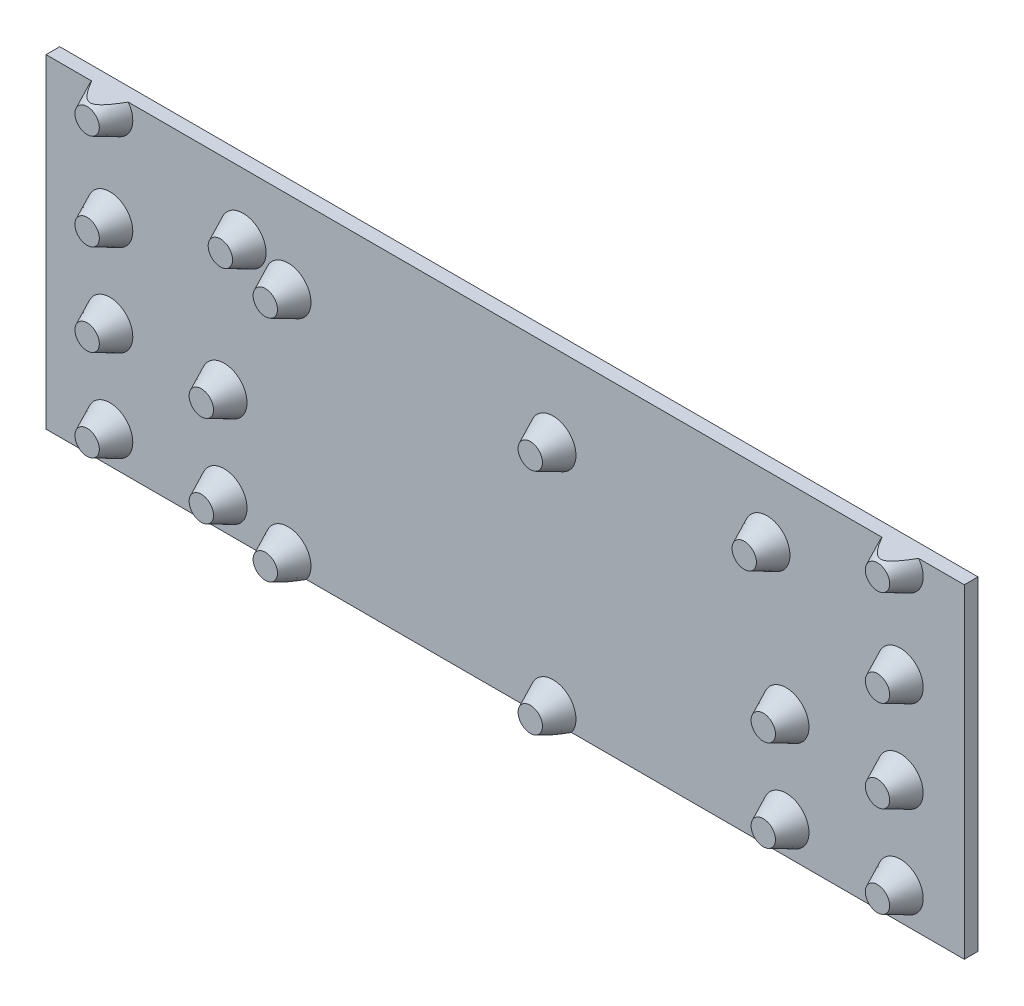
SolidWorks part; units mm, degrees
ref_plane "Plan de face" through (0, 0, 0) normal (0, 0, 1) x (1, 0, 0)
ref_plane "Plan de dessus" through (0, 0, 0) normal (0, 1, 0) x (1, 0, 0)
ref_plane "Plan de droite" through (0, 0, 0) normal (1, 0, 0) x (0, 0, -1)
sketch "Esquisse2" plane through (0, 0, 0) normal (0, 0, 1) x (1, 0, 0)
  line L1 (-100.0531, 29.2995) -> (100.9469, 29.2995)
  line L2 (-100.0531, 29.2995) -> (-100.0531, -45.7005)
  line L3 (-100.0531, -45.7005) -> (100.9469, -45.7005)
  line L4 (100.9469, 29.2995) -> (100.9469, -45.7005)
  dimension "D1" = 201
  dimension "7.5" = 75
extrude "Boss.-Extru.1" add sketch "Esquisse2" along normal blind 3
sketch "Esquisse3" plane through (0, 0, 3) normal (0, 0, 1) x (1, 0, 0)
  line L0 (100.9469, -45.7005) -> (100.9469, 29.2995) construction
  line L1 (-100.0531, -45.7005) -> (100.9469, -45.7005) construction
  line L3 (-100.0531, 29.2995) -> (-100.0531, -45.7005) construction
  line L4 (100.9469, 29.2995) -> (-100.0531, 29.2995) construction
  circle A0 centre (-47.0531, 9.2995) radius 5
  circle A1 centre (-47.0531, -40.7005) radius 5
  circle A2 centre (10.9469, 9.3007) radius 5
  circle A3 centre (10.9469, -40.6993) radius 5
  circle A5 centre (-86.0531, 24.2995) radius 5
  circle A6 centre (-56.8855, 13.7995) radius 5
  circle A7 centre (-86.0531, 3.2995) radius 5
  circle A9 centre (-86.0531, -16.7005) radius 5
  circle A10 centre (-86.0531, -36.7005) radius 5
  circle A11 centre (-61.0531, -16.7005) radius 5
  circle A12 centre (-61.0531, -36.7005) radius 5
  circle A13 centre (86.9469, 24.2994) radius 5
  circle A14 centre (86.9469, 3.2995) radius 5
  circle A15 centre (57.7792, 13.7994) radius 5
  circle A16 centre (86.9469, -16.7005) radius 5
  circle A17 centre (86.9469, -36.7005) radius 5
  circle A18 centre (61.9469, -36.7005) radius 5
  circle A19 centre (61.9469, -16.7005) radius 5
  point P4 (100.9469, -8.2005)
  dimension "D1" = 148
  dimension "D3" = 50
  dimension "D5" = 58
  dimension "D6" = 58
  dimension "D8" = 14
  dimension "D10" = 21
  dimension "D13" = 20
  dimension "D14" = 20
  dimension "D17" = 25
  dimension "D18" = 20
  dimension "D21" = 14
  dimension "D23" = 31
  dimension "D25" = 14
  dimension "D27" = 20
  dimension "D28" = 25
  dimension "D33" = 25
  dimension "D2" = 55
  dimension "D4" = 148
  dimension "D7" = 50
  dimension "D9" = 5
  dimension "D11" = 31
  dimension "D12" = 31
  dimension "D15" = 14
  dimension "D16" = 14
  dimension "D19" = 25
  dimension "D20" = 14
  dimension "D22" = 20.9998
  dimension "D24" = 31
  dimension "D26" = 20
  dimension "D29" = 9
  dimension "D30" = 9
  dimension "D31" = 9
  dimension "D32" = 9
  dimension "D34" = 20
extrude "Boss.-Extru.3" add sketch "Esquisse3" along normal blind 5 draft 25
sketch "Esquisse4" plane through (0, 29.2995, 0) normal (0, 1, 0) x (1, 0, 0)
  line L1 (106.4185, 0) -> (-103.5815, 0)
  line L2 (106.4185, 0) -> (106.4185, -11.156)
  line L3 (106.4185, -11.156) -> (-103.5815, -11.156)
  line L4 (-103.5815, 0) -> (-103.5815, -11.156)
  dimension "D1" = 210
extrude "Enlèv. mat.-Extru.1" cut sketch "Esquisse4" against normal blind 2
sketch "Esquisse5" plane through (0, -45.7005, 0) normal (0, -1, 0) x (-1, 0, 0)
  line L1 (-109.9469, 0) -> (110.0531, 0)
  line L2 (-109.9469, 0) -> (-109.9469, -18.9276)
  line L3 (-109.9469, -18.9276) -> (110.0531, -18.9276)
  line L4 (110.0531, 0) -> (110.0531, -18.9276)
  dimension "D1" = 220
  dimension "D2" = 18.9276
  dimension "D3" = 10
extrude "Enlèv. mat.-Extru.2" cut sketch "Esquisse5" against normal blind 2
